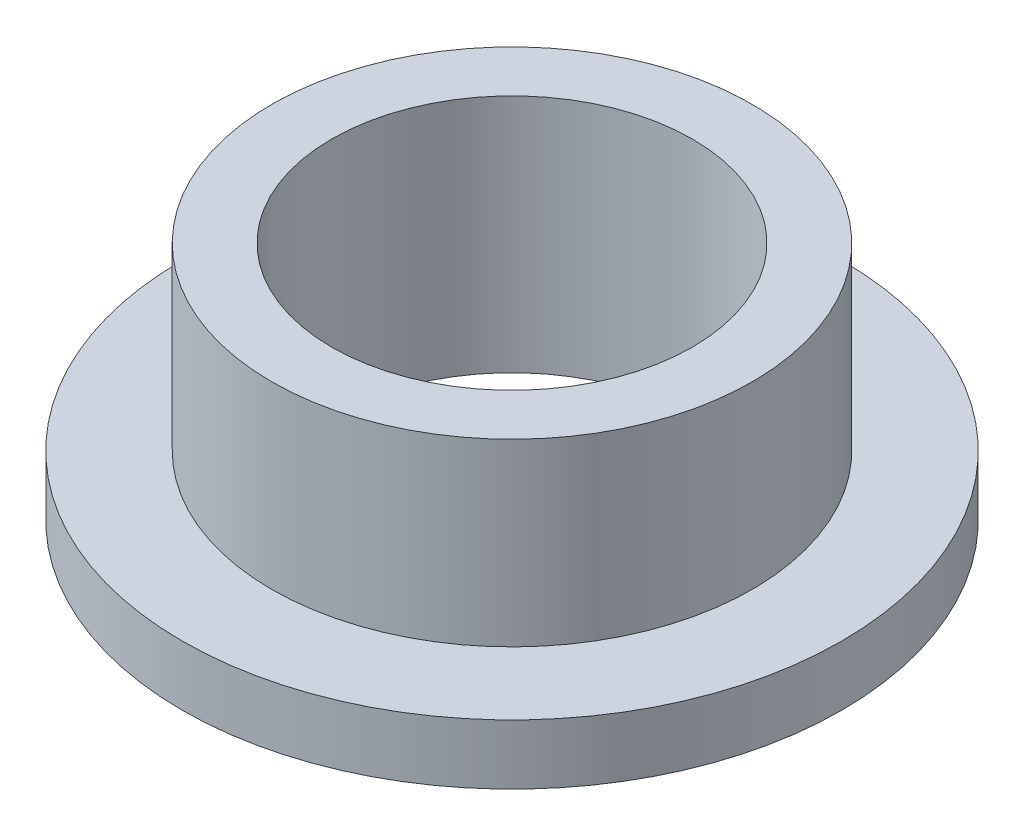
SolidWorks part; units mm, degrees
ref_plane "Front" through (0, 0, 0) normal (0, 0, 1) x (1, 0, 0)
ref_plane "Top" through (0, 0, 0) normal (0, 1, 0) x (1, 0, 0)
ref_plane "Right" through (0, 0, 0) normal (1, 0, 0) x (0, 0, -1)
sketch "Sketch1" plane through (0, 0, 0) normal (0, 1, 0) x (1, 0, 0)
  circle A0 centre (0, 0) radius 4.7752
  circle A1 centre (0, 0) radius 6.3627
  circle A2 centre (0, 0) radius 8.7312
  dimension "ID" = 9.5504
  dimension "OD" = 12.7254
  dimension "FlangeOD" = 17.4625
sketch "Sketch2" plane through (0, 0, 0) normal (0, 1, 0) x (1, 0, 0)
  circle A0 centre (0, 0) radius 4.7752 construction
  circle A1 centre (0, 0) radius 6.3627 construction
  circle A2 centre (0, 0) radius 4.7752
  circle A3 centre (0, 0) radius 6.3627
extrude "Boss-Extrude1" add sketch "Sketch2" along normal blind 6.35
sketch "Sketch3" plane through (0, 0, 0) normal (0, 1, 0) x (1, 0, 0)
  circle A0 centre (0, 0) radius 8.7312 construction
  circle A1 centre (0, 0) radius 6.3627 construction
  circle A2 centre (0, 0) radius 8.7312
  circle A3 centre (0, 0) radius 6.3627
extrude "Boss-Extrude2" add sketch "Sketch3" along normal blind 1.5875
